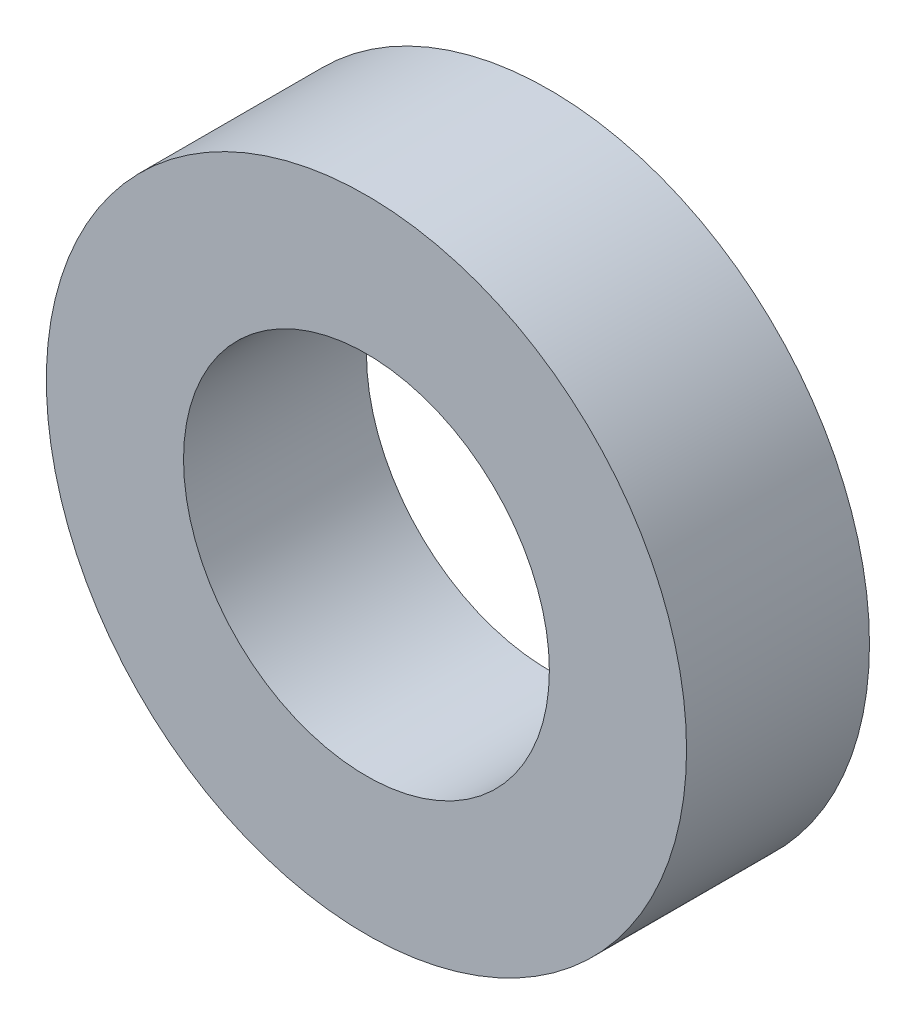
SolidWorks part; units mm, degrees
ref_plane "前视基准面" through (0, 0, 0) normal (0, 0, 1) x (1, 0, 0)
ref_plane "上视基准面" through (0, 0, 0) normal (0, 1, 0) x (1, 0, 0)
ref_plane "右视基准面" through (0, 0, 0) normal (1, 0, 0) x (0, 0, -1)
sketch "草图1" plane through (0, 0, 0) normal (0, 0, 1) x (1, 0, 0)
  circle A0 centre (0, 0) radius 4
  circle A1 centre (0, 0) radius 7
  dimension "D1" = 8
  dimension "D2" = 14
extrude "凸台-拉伸1" add sketch "草图1" along normal mid plane 4
